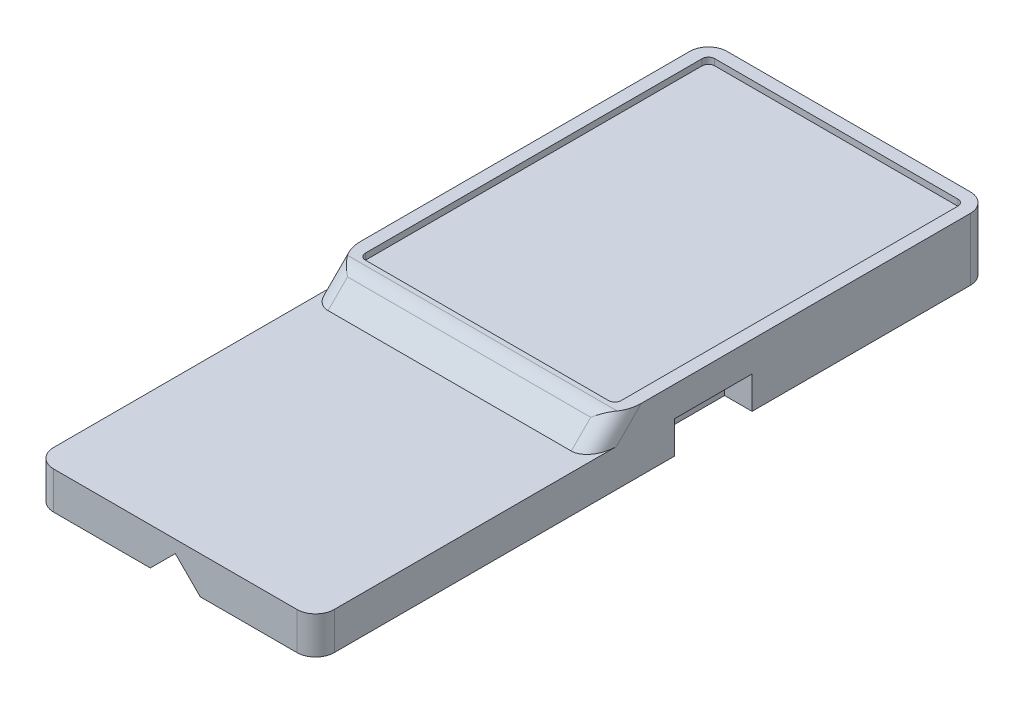
SolidWorks part; units mm, degrees
ref_plane "Спереди" through (0, 0, 0) normal (0, 0, 1) x (1, 0, 0)
ref_plane "Сверху" through (0, 0, 0) normal (0, 1, 0) x (1, 0, 0)
ref_plane "Справа" through (0, 0, 0) normal (1, 0, 0) x (0, 0, -1)
sketch "surface_sketch" plane through (0, 0, 0) normal (0, 1, 0) x (1, 0, 0)
  line L2 (-12.4, -15) -> (10.1, -15)
  line L3 (10.1, -15) -> (10.1, 15)
  line L4 (0.1, 0) -> (0.1, -15) construction
  line L5 (0.1, 0) -> (10.1, 0) construction
  line L7 (-12.4, 15) -> (10.1, 15)
  line L8 (-12.4, 15) -> (-12.4, -15)
  line L9 (-3.65, -15) -> (-3.65, -7.5) construction
  line L10 (-3.65, -7.5) -> (0.1, -7.5) construction
  line L11 (-3.65, -7.5) -> (-3.65, 0) construction
  line L12 (-3.65, 0) -> (-3.65, 7.5) construction
  line L13 (-1.3, 7.5) -> (-6, 7.5)
  line L14 (-6, 0) -> (-1.3, 0)
  line L15 (-6, -7.5) -> (-1.3, -7.5)
  line L16 (6.2, -7.5) -> (1.5, -7.5)
  line L17 (6.2, 0) -> (1.5, 0) construction
  line L18 (3.85, 7.5) -> (1.5, 7.5)
  line L19 (0, 0) -> (0.1, 0) construction
  line L20 (3.85, 7.5) -> (6.2, 7.5)
  circle A0 centre (-3.65, 7.5) radius 2.35
  circle A1 centre (-3.65, 0) radius 2.35
  circle A2 centre (-3.65, -7.5) radius 2.35
  circle A3 centre (3.85, -7.5) radius 2.35
  circle A4 centre (3.85, 0) radius 2.35
  circle A5 centre (3.85, 7.5) radius 2.35
  dimension "D1" = 22.5
  dimension "D9" = 4.7
  dimension "D10" = 4.7
  dimension "D11" = 4.7
  dimension "D2" = 30
  dimension "D5" = 7.5
  dimension "D6" = 3.75
  dimension "D7" = 7.5
  dimension "D8" = 7.5
  dimension "D3" = 10
  dimension "D4" = 0.1
extrude "body" add sketch "surface_sketch" against normal blind 4.5
ref_plane "midplane" through (-1.15, 0, 0) normal (1, 0, 0) x (0, 0, -1)
sketch "Эскиз19" plane through (0, -4.5, 0) normal (0, 1, 0) x (1, 0, 0)
  line L1 (-12.4, -15) -> (10.1, -15)
  line L2 (-12.4, -15) -> (-12.4, -39)
  line L3 (-12.4, -39) -> (10.1, -39)
  line L4 (10.1, -15) -> (10.1, -39)
  dimension "D1" = 22.5
  dimension "D2" = 24
extrude "Бобышка-Вытянуть4" add sketch "Эскиз19" along normal blind 3
fillet "Скругление6" radius 1.5 4 edges at (10.1, -3, 39) (-12.4, -3, 39) (10.1, -2.25, -15) (-12.4, -2.25, -15)
sketch "magnet_cutout_sketch" plane through (0, -4.5, 0) normal (0, -1, 0) x (1, 0, 0)
  line L0 (10.1, 37.5) -> (10.1, -13.5) construction
  line L1 (7.9, 10.2) -> (10.1, 10.2)
  line L2 (7.9, 10.2) -> (7.9, 4)
  line L3 (7.9, 4) -> (10.1, 4)
  line L4 (10.1, 10.2) -> (10.1, 4)
  line L5 (9, 4) -> (9, 10.2) construction
  line L6 (7.9, 7.1) -> (10.1, 7.1) construction
  line L9 (7.9, 4) -> (7.9, -15) construction
  line L10 (-10.9, -15) -> (8.6, -15) construction
  point P0 (9, 7.1)
  dimension "D1" = 2.2
  dimension "D2" = 6.2
  dimension "D3" = 19
extrude "magnet_cutout" cut sketch "magnet_cutout_sketch" against normal blind 2.6
mirror "magnet_cutout_mirror" about plane through (-1.15, 0, 0) normal (1, 0, 0) of "magnet_cutout"
sketch "border_sketch" plane through (0, 0, 0) normal (0, 1, 0) x (1, 0, 0)
  line L0 (-12.4, -15) -> (-12.4, 13.5)
  line L1 (10.1, -15) -> (10.1, 13.5)
  line L2 (8.6, 15) -> (-10.9, 15)
  line L4 (-1.15, 15) -> (-1.15, -15.5) construction
  line L5 (-12.4, -0.75) -> (10.1, -0.75) construction
  line L6 (-10.9, 15) -> (8.6, 15) construction
  line L7 (10.1, -15) -> (10.1, 13.5) construction
  arc A2 (10.1, 13.5) -> (8.6, 15) centre (8.6, 13.5) ccw
  arc A3 (-12.4, 13.5) -> (-10.9, 15) centre (-10.9, 13.5) cw
  dimension "D1" = 1.5
extrude "border" add sketch "border_sketch" along normal blind 0.5 thin contours L0 A3 L2 A2 L1
sketch "Эскиз21" plane through (-12.4, 0, 0) normal (-1, 0, 0) x (0, 0, 1)
  line L0 (15, 0.5) -> (17, -1.5)
  line L1 (15, -1.5) -> (37.5, -1.5) construction
  line L2 (17, -1.5) -> (15, -1.5)
  line L3 (15, -1.5) -> (14, -1.5)
  line L4 (14, -1.5) -> (14, 0.5)
  line L5 (15, 0.5) -> (-13.5, 0.5) construction
  line L6 (14, 0.5) -> (15, 0.5)
  line L7 (15, 0.5) -> (15, -1.5) construction
  dimension "D1" = 1
extrude "champfer" add sketch "Эскиз21" against normal up to surface (22.5 mm away) up to face at (10.1, -2.38, 10.64)
fillet "Скругление7" radius 1.5 2 edges at (10.1, -0.5, 16) (-12.4, -0.5, 16)
fillet "Скругление8" radius 0.5 2 edges at (-11.4, 0.25, 14) (9.1, 0.25, 14)
sketch "Эскиз22" plane through (-12.4, 0, 0) normal (-1, 0, 0) x (0, 0, 1)
  line L0 (12.8787, 0.5) -> (14.3787, 0.5)
  line L1 (15.4393, 0.0607) -> (17, -1.5)
  line L2 (17, -1.5) -> (17.9233, -1.5)
  line L3 (14.8787, -1.5) -> (37.5, -1.5) construction
  line L4 (17.9233, -1.5) -> (15.1812, 1.2421)
  line L5 (15.1812, 1.2421) -> (12.8787, 1.1224)
  line L6 (12.8787, 1.1224) -> (12.8787, 0.5)
  arc A0 (15.4393, 0.0607) -> (14.3787, 0.5) centre (14.3787, -1) ccw
  point P13 (15, 0.5)
  dimension "D1" = 1.5
extrude "Вырез-Вытянуть1" cut sketch "Эскиз22" against normal through all
sketch "Эскиз23" plane through (0, 0, -15) normal (0, 0, -1) x (-1, 0, 0)
  line L0 (1.15, -4.5) -> (1.15, -2.5) construction
  line L1 (10.9, -4.5) -> (-8.6, -4.5) construction
  line L2 (1.15, -4.5) -> (-0.85, -4.5)
  line L3 (-0.85, -4.5) -> (1.15, -2.5)
  line L4 (1.15, -2.5) -> (3.15, -4.5)
  line L5 (3.15, -4.5) -> (1.15, -4.5)
  dimension "D1" = 2
  dimension "D2" = 2
  dimension "D3" = 2
extrude "Вырез-Вытянуть2" cut sketch "Эскиз23" against normal through all both and the other way through all
equation "\"hole_diam\"= 4.7мм"
equation "\"cell_width\"= \"cell_pace\""
equation "\"cell_pace\"= 22.5мм'distance between neighbouring cells"
equation "\"holes_horisontal_dist\"= 7.5"
equation "\"holes_vertical_dist\"= \"holes_horisontal_dist\""
equation "\"cell_length\"= \"holes_vertical_dist\" * 4"
equation "\"char_width\"= 15"
equation "\"char_thickness\"= 2.5"
equation "\"char_height\"= 22"
equation "\"D1@body\" = \"cell_surface_height\""
equation "\"char_champfer_width\"= 1"
equation "\"char_depth\"= 1.5"
equation "\"D1@Эскиз19\"=\"cell_width\""
equation "\"D2@surface_sketch\"=\"cell_length\""
equation "\"D9@surface_sketch\"=\"hole_diam\""
equation "\"D8@surface_sketch\"=\"holes_vertical_dist\""
equation "\"D6@surface_sketch\"=\"holes_horisontal_dist\"/2"
equation "\"D1@surface_sketch\"=\"cell_width\""
equation "\"D5@surface_sketch\"=\"holes_vertical_dist\""
equation "\"D7@surface_sketch\"=\"holes_vertical_dist\""
equation "\"magnet_cut_height\"= 2.6"
equation "\"magnet_cut_width\"= 6.2"
equation "\"magnet_cut_depth\"= 2.2"
equation "\"D1@magnet_cutout_sketch\" = \"magnet_cut_depth\""
equation "\"D2@magnet_cutout_sketch\" = \"magnet_cut_width\""
equation "\"D1@magnet_cutout\" = \"magnet_cut_height\""
equation "\"border_width\"= 1"
equation "\"border_height\"= 0.5"
equation "\"D1\"= \"border_height\""
equation "\"D5@border\" = \"border_width\""
equation "\"D2@back_complementary_holes_sketch\" = \"hole_diam\" - 0.2"
equation "\"D3@back_complementary_holes_sketch\" = \"holes_vertical_dist\""
equation "\"D4@back_complementary_holes_sketch\" = \"holes_horisontal_dist\" / 2"
equation "\"D5@back_complementary_holes_sketch\" = \"holes_vertical_dist\""
equation "\"D6@back_complementary_holes_sketch\" = \"holes_vertical_dist\""
equation "\"D7@back_complementary_holes_sketch\" = \"hole_diam\" - 0.2"
equation "\"D8@back_complementary_holes_sketch\" = \"hole_diam\" - 0.2"
